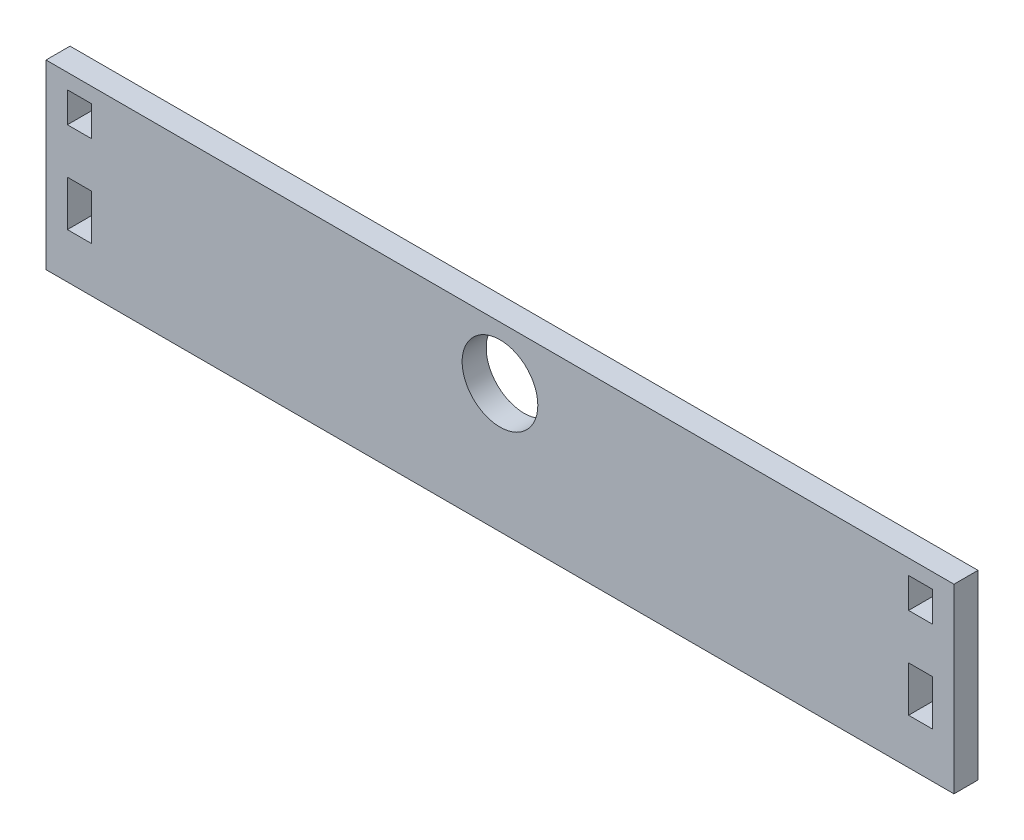
SolidWorks part; units mm, degrees
ref_plane "Front Plane" through (0, 0, 0) normal (0, 0, 1) x (1, 0, 0)
ref_plane "Top Plane" through (0, 0, 0) normal (0, 1, 0) x (1, 0, 0)
ref_plane "Right Plane" through (0, 0, 0) normal (1, 0, 0) x (0, 0, -1)
ref_plane "Plane1"
sketch "Sketch1" plane through (0, 0, 0) normal (0, 0, 1) x (1, 0, 0)
  line L0 (57, -1) -> (-3, -1)
  line L1 (-3, -1) -> (-3, 11)
  line L2 (-3, 11) -> (57, 11)
  line L3 (57, 11) -> (57, -1)
  line L4 (54, 10) -> (55.5875, 10)
  line L5 (55.5875, 10) -> (55.5875, 8)
  line L6 (55.5875, 8) -> (54, 8)
  line L7 (54, 8) -> (54, 10)
  line L8 (0, 10) -> (-1.5875, 10)
  line L9 (-1.5875, 10) -> (-1.5875, 8)
  line L10 (-1.5875, 8) -> (0, 8)
  line L11 (0, 8) -> (0, 10)
  line L12 (0, 5) -> (-1.5875, 5)
  line L13 (-1.5875, 5) -> (-1.5875, 2)
  line L14 (-1.5875, 2) -> (0, 2)
  line L15 (0, 2) -> (0, 5)
  line L16 (54, 5) -> (55.5875, 5)
  line L17 (55.5875, 5) -> (55.5875, 2)
  line L18 (55.5875, 2) -> (54, 2)
  line L19 (54, 2) -> (54, 5)
  dimension "D1" = 54
  dimension "D2" = 2
  dimension "D3" = 1.5875
  dimension "D4" = 3
  dimension "D5" = 1.5875
  dimension "D6" = 3
  dimension "D7" = 60
  dimension "D8" = 12
extrude "Extrusion1" add sketch "Sketch1" along normal blind 1.5875 contours L3 L2 L1 L0 L15 L14 L13 L12 L11 L10 L9 L8 L6 L7 L4 L5 L18 L19 L16 L17
sketch "Sketch2" plane through (0, 0, 1.5875) normal (0, 0, 1) x (1, 0, 0)
  circle A0 centre (27, 7.4899) radius 2.5
  dimension "D1" = 5
extrude "Extrusion2" cut sketch "Sketch2" against normal up to surface (1.5875 mm away) up to face at (-0.7937, 3.5, 0)
